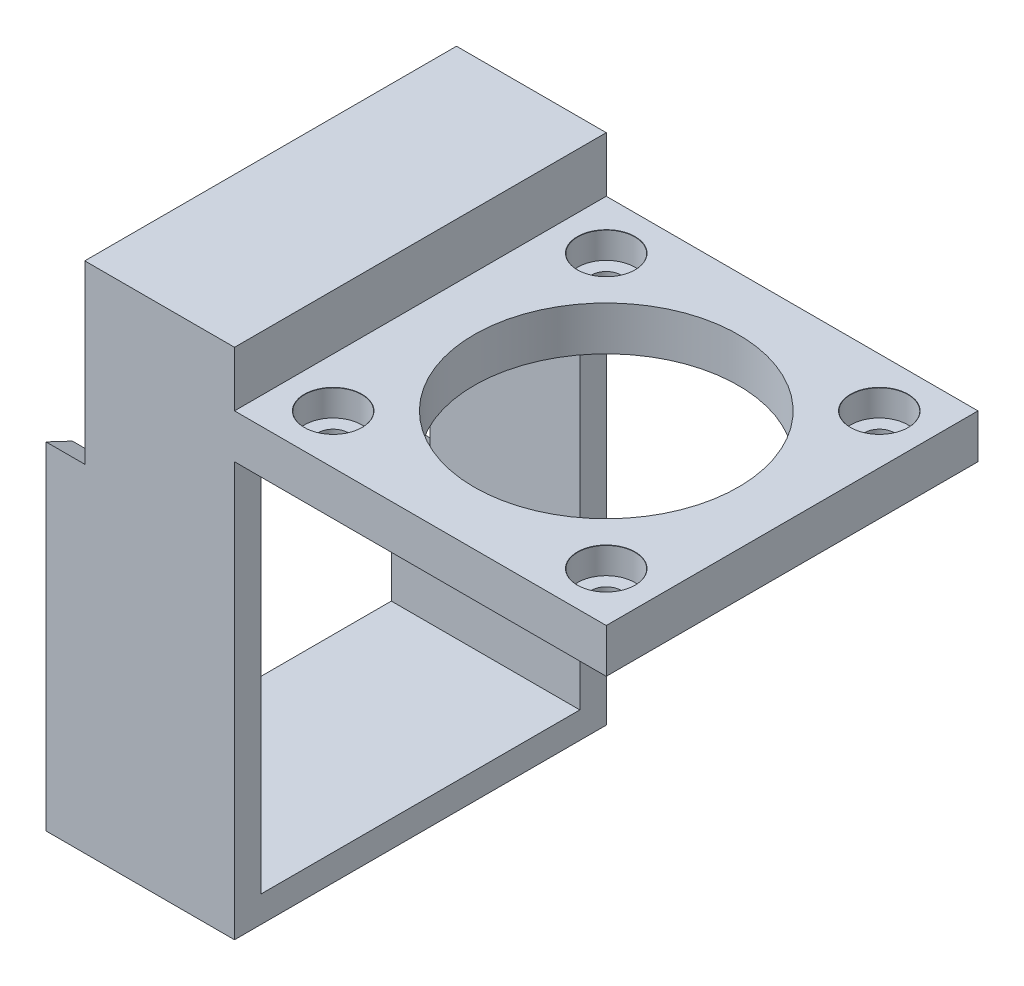
SolidWorks part; units mm, degrees
ref_plane "Front Plane" through (0, 0, 0) normal (0, 0, 1) x (1, 0, 0)
ref_plane "Top Plane" through (0, 0, 0) normal (0, 1, 0) x (1, 0, 0)
ref_plane "Right Plane" through (0, 0, 0) normal (1, 0, 0) x (0, 0, -1)
sketch "Sketch1" plane through (0, 0, 0) normal (1, 0, 0) x (0, 0, -1)
  line L0 (-41.2795, 58.25) -> (41.2795, 58.25) construction
  line L1 (-21.1, 58.25) -> (21.1, 58.25)
  line L2 (-21.1, 58.25) -> (-21.1, 0)
  line L3 (-21.1, 0) -> (21.1, 0)
  line L4 (21.1, 58.25) -> (21.1, 0)
  line L5 (21.1, 47) -> (21.1, 38.9) construction
  point P6 (0, 58.25)
extrude "Boss-Extrude1" add sketch "Sketch1" along normal up to surface (17 mm away)
sketch "Sketch2" plane through (17, 0, 0) normal (1, 0, 0) x (0, 0, -1)
  line L0 (-21.1, 58.25) -> (-21.1, 0) construction
  line L1 (-21.1, 52) -> (21.1, 52)
  line L2 (-21.1, 52) -> (-21.1, 47)
  line L3 (-21.1, 47) -> (21.1, 47)
  line L4 (21.1, 52) -> (21.1, 47)
  dimension "D1" = 5
extrude "Boss-Extrude2" add sketch "Sketch2" along normal up to surface (42.2 mm away)
sketch "Sketch3" plane through (0, 52, 0) normal (0, 1, 0) x (1, 0, 0)
  circle A0 centre (53.6, -15.5) radius 1.275 construction
  circle A1 centre (53.6, 15.5) radius 1.275 construction
  circle A2 centre (53.6, -15.5) radius 1.275
  circle A3 centre (53.6, 15.5) radius 1.275
  circle A4 centre (22.6, 15.5) radius 1.275 construction
  circle A5 centre (22.6, 15.5) radius 1.275
  circle A6 centre (22.6, -15.5) radius 1.275 construction
  circle A7 centre (22.6, -15.5) radius 1.275
  point P0 (53.6, -15.5)
  point P2 (53.6, 15.5)
  point P6 (22.6, 15.5)
  point P9 (22.6, -15.5)
hole_wizard "CBORE for M3 SHCS1" positions "Sketch3" profile "Sketch4" counterbore size "M3" standard "ANSI Metric" end condition through all
sketch "Sketch4" plane through (53.6, 52, 15.5) normal (1, 0, 0) x (0, 0, 1)
  line L0 (0, 0) -> (0, 52)
  line L1 (0, 52) -> (1.7, 52)
  line L3 (1.7, 52) -> (1.7, 3)
  line L4 (3.25, 3) -> (1.7, 3)
  line L5 (3.25, 3) -> (3.25, 0.025)
  line L6 (3.25, 0.025) -> (3.275, 0)
  line L7 (3.275, 0) -> (0, 0)
  line L8 (-3.25, 0.025) -> (-3.275, 0) construction
  line L11 (0, -6.35) -> (0, 107.95) construction
  dimension "Thru Hole Dia." = 3.4
  dimension "Thru Hole Depth" = 52
  dimension "C'Bore Dia." = 6.5
  dimension "C'Bore Depth" = 3
  dimension "Near C'Sink Dia." = 6.55
  dimension "Near C'Sink Angle" = 90
sketch "Sketch5" plane through (0, 52, 0) normal (0, 1, 0) x (1, 0, 0)
  circle A0 centre (38.1, 0) radius 15
  dimension "D1" = 30
extrude "Cut-Extrude1" cut sketch "Sketch5" against normal through all
sketch "Sketch6" plane through (0, 0, 0) normal (1, 0, 0) x (0, 0, -1)
  line L0 (-21.1, 38.25) -> (21.1, 18.25)
  line L2 (21.1, 52) -> (21.1, 47) construction
  line L3 (21.1, 58.25) -> (-21.1, 58.25) construction
  line L4 (21.1, 18.25) -> (21.1, 0)
  line L5 (21.1, 0) -> (-21.1, 0)
  line L6 (-21.1, 0) -> (-21.1, 38.25)
  line L7 (-21.1, 58.25) -> (-21.1, 0) construction
  line L8 (-21.1, 0) -> (21.1, 0) construction
  dimension "D1" = 20
  dimension "D2" = 40
extrude "Boss-Extrude3" add sketch "Sketch6" against normal blind 4.4
sketch "Sketch7" plane through (17, 0, 0) normal (1, 0, 0) x (0, 0, -1)
  line L0 (21.1, 58.25) -> (-21.1, 58.25) construction
  line L1 (-18.1, 44.25) -> (18.1, 44.25)
  line L2 (-18.1, 44.25) -> (-18.1, 3)
  line L3 (-18.1, 3) -> (18.1, 3)
  line L4 (18.1, 44.25) -> (18.1, 3)
  line L5 (21.1, 52) -> (21.1, 47) construction
  line L6 (-21.1, 47) -> (-21.1, 52) construction
  line L7 (-21.1, 0) -> (21.1, 0) construction
  dimension "D1" = 14
  dimension "D2" = 3
  dimension "D3" = 3
  dimension "D4" = 3
extrude "Cut-Extrude2" cut sketch "Sketch7" against normal through all
